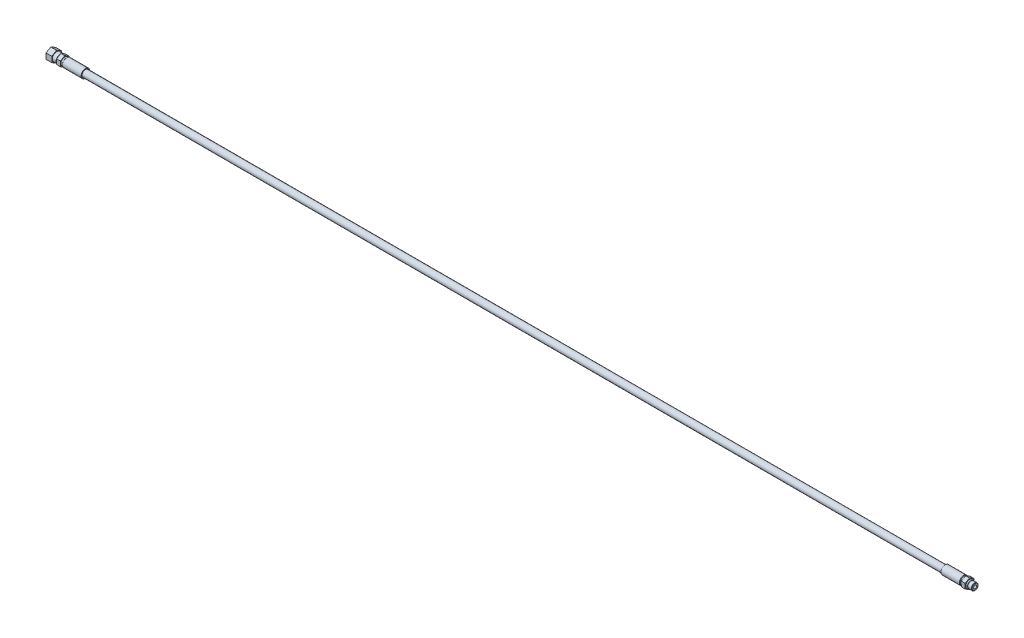
SolidWorks part; units mm, degrees
material "Alloy Steel"
ref_plane "Front Plane" through (0, 0, 0) normal (0, 0, 1) x (1, 0, 0)
ref_plane "Top Plane" through (0, 0, 0) normal (0, 1, 0) x (1, 0, 0)
ref_plane "Right Plane" through (0, 0, 0) normal (1, 0, 0) x (0, 0, -1)
sketch "Sketch1" plane through (0, 0, 0) normal (0, 0, 1) x (1, 0, 0)
  line L0 (0, 0) -> (77.1442, 0) construction
  line L1 (-1524, 2.413) -> (0, 2.413)
  line L2 (0, 2.413) -> (0, 5.5372)
  line L3 (0, 5.5372) -> (-6.3246, 5.5372)
  line L4 (-6.3246, 5.5372) -> (-7.239, 4.6228)
  line L5 (-7.239, 4.6228) -> (-9.144, 4.6228)
  line L6 (-9.144, 4.6228) -> (-9.144, 19.05)
  line L7 (-9.144, 19.05) -> (-15.494, 19.05)
  line L8 (-15.494, 19.05) -> (-15.494, 6.35)
  line L9 (-15.494, 6.35) -> (-18.034, 6.35)
  line L10 (-18.034, 6.35) -> (-18.796, 7.112)
  line L11 (-18.796, 7.112) -> (-49.276, 7.112)
  line L12 (-49.276, 7.112) -> (-49.276, 5.588)
  line L13 (-49.276, 5.588) -> (-1466.85, 5.588)
  line L14 (-1466.85, 5.588) -> (-1466.85, 7.112)
  line L15 (-1466.85, 7.112) -> (-1497.711, 7.112)
  line L16 (-1497.711, 7.112) -> (-1498.473, 6.35)
  line L17 (-1498.473, 6.35) -> (-1501.013, 6.35)
  line L18 (-1501.013, 6.35) -> (-1501.013, 19.05)
  line L19 (-1501.013, 19.05) -> (-1507.363, 19.05)
  line L20 (-1507.363, 19.05) -> (-1507.363, 6.35)
  line L21 (-1507.363, 6.35) -> (-1508.125, 6.35)
  line L22 (-1508.125, 6.35) -> (-1508.125, 7.112)
  line L23 (-1508.125, 7.112) -> (-1514.475, 7.112)
  line L24 (-1514.475, 7.112) -> (-1514.475, 19.05)
  line L25 (-1514.475, 19.05) -> (-1524, 19.05)
  line L26 (-1524, 19.05) -> (-1524, 2.413)
  dimension "D1" = 4.826
  dimension "D2" = 11.0744
  dimension "D3" = 9.144
  dimension "D4" = 1.905
  dimension "D5" = 45
  dimension "D6" = 9.2456
  dimension "D7" = 11.176
  dimension "D8" = 14.224
  dimension "D9" = 2.54
  dimension "D10" = 12.7
  dimension "D11" = 45
  dimension "D12" = 6.35
  dimension "D13" = 38.1
  dimension "D14" = 30.48
  dimension "D15" = 45
  dimension "D16" = 30.861
  dimension "D17" = 9.525
  dimension "D18" = 38.1
  dimension "D19" = 6.35
  dimension "D20" = 1524
  dimension "D21" = 0.762
  dimension "D22" = 6.35
  dimension "D23" = 1417.574
revolve "Revolve1" add sketch "Sketch1" angle 360 about L0
sketch "Sketch2" plane through (-9.144, 0, 0) normal (1, 0, 0) x (0, 0, -1)
  line L1 (0, 8.2122) -> (-7.112, 4.1061)
  line L2 (-7.112, 4.1061) -> (-7.112, -4.1061)
  line L3 (-7.112, -4.1061) -> (0, -8.2122)
  line L4 (0, -8.2122) -> (7.112, -4.1061)
  line L5 (7.112, -4.1061) -> (7.112, 4.1061)
  line L6 (7.112, 4.1061) -> (0, 8.2122)
  circle A0 centre (0, 0) radius 7.112 construction
  circle A1 centre (0, 0) radius 19.05 construction
  circle A2 centre (0, 0) radius 19.05
  dimension "D1" = 14.224
extrude "Cut-Extrude1" cut sketch "Sketch2" against normal up to surface (1498.219 mm away) up to face at (-1507.363, 0, 6.35)
sketch "Sketch3" plane through (-1524, 0, 0) normal (-1, 0, 0) x (0, 0, 1)
  line L1 (0, 9.1654) -> (-7.9375, 4.5827)
  line L2 (-7.9375, 4.5827) -> (-7.9375, -4.5827)
  line L3 (-7.9375, -4.5827) -> (0, -9.1654)
  line L4 (0, -9.1654) -> (7.9375, -4.5827)
  line L5 (7.9375, -4.5827) -> (7.9375, 4.5827)
  line L6 (7.9375, 4.5827) -> (0, 9.1654)
  circle A0 centre (0, 0) radius 7.9375 construction
  circle A1 centre (0, 0) radius 19.05 construction
  circle A2 centre (0, 0) radius 19.05
  dimension "D1" = 15.875
extrude "Cut-Extrude2" cut sketch "Sketch3" against normal up to next
chamfer "Chamfer1" distance 0.6858 angle 45 1 edges at (0, 0, 5.5372)
sketch "Sketch4" plane through (0, 0, 0) normal (0, 0, 1) x (1, 0, 0)
  line L0 (0, 0) -> (16.2539, 0) construction
  line L1 (-9.144, 8.2122) -> (-9.144, 4.1061) construction
  circle A0 centre (-8.128, 5.588) radius 1.016
  dimension "D2" = 2.032
  dimension "D1" = 11.176
revolve "Revolve5" add sketch "Sketch4" angle 360 about L0
sketch "Sketch5" plane through (0, 0, 0) normal (0, 0, 1) x (1, 0, 0)
  line L0 (-576.4898, 0) -> (-618.5875, 0) construction
  line L1 (-1524, 6.1999) -> (-1522.7607, 4.9606)
  line L2 (-1524, 4.5827) -> (-1524, 9.1654) construction
  line L3 (-1522.7607, 4.9606) -> (-1511.3, 4.9606)
  line L4 (-1511.3, 4.9606) -> (-1508.3194, 0)
  line L5 (-1508.3194, 0) -> (-1524, 0)
  line L6 (-1524, 0) -> (-1524, 6.1999)
  dimension "D1" = 45
  dimension "D2" = 1.7526
  dimension "D3" = 9.9212
  dimension "D4" = 59
  dimension "D5" = 12.7
revolve "Cut-Revolve2" cut sketch "Sketch5" angle 360 about L0
